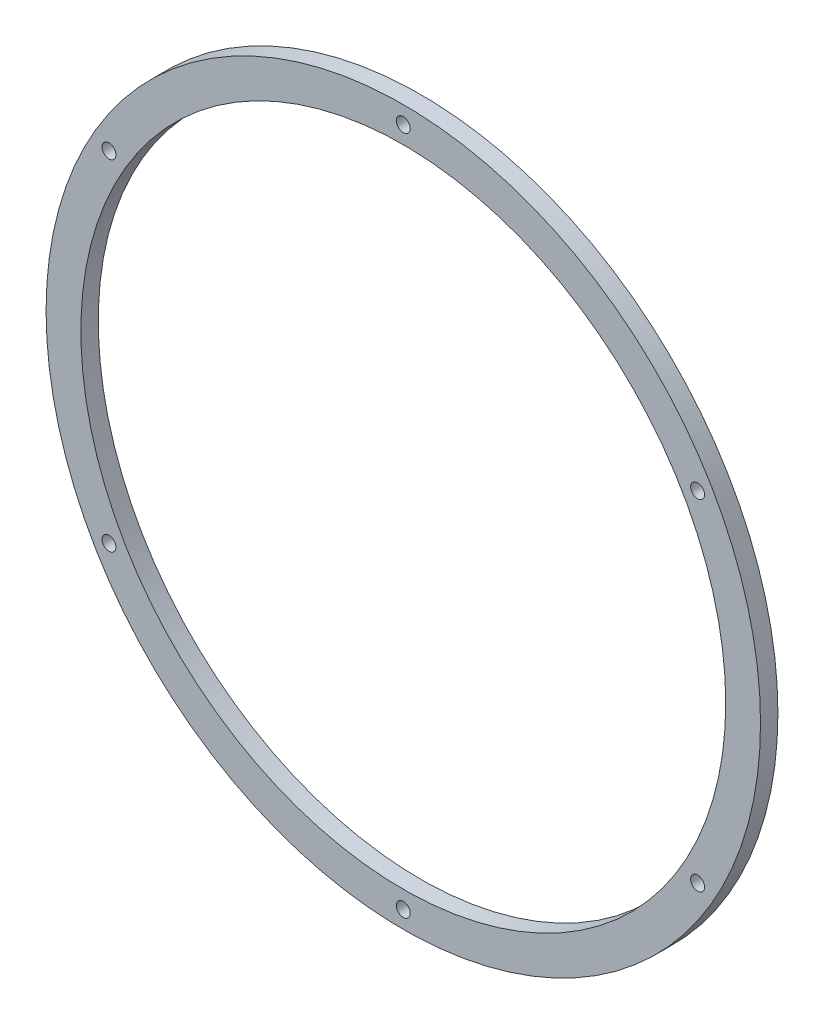
SolidWorks part; units mm, degrees
material "Brass"
ref_plane "Front Plane" through (0, 0, 0) normal (0, 0, 1) x (1, 0, 0)
ref_plane "Top Plane" through (0, 0, 0) normal (0, 1, 0) x (1, 0, 0)
ref_plane "Right Plane" through (0, 0, 0) normal (1, 0, 0) x (0, 0, -1)
sketch "Sketch1" plane through (0, 0, 0) normal (0, 0, 1) x (1, 0, 0)
  circle A0 centre (0, 0) radius 185.4
  circle A1 centre (0, 0) radius 205.4
  dimension "D1" = 370.8
  dimension "D2" = 410.8
extrude "Body" add sketch "Sketch1" along normal mid plane 10
sketch "Sketch2" plane through (0, 0, 5) normal (0, 0, 1) x (1, 0, 0)
  line L0 (0, -71.4075) -> (0, 70.4111) construction
  circle A0 centre (0, 195.4) radius 4
  circle A1 centre (0, 0) radius 195.4 construction
  dimension "D1" = 8
  dimension "D2" = 390.8
extrude "Cut-Extrude1" cut sketch "Sketch2" against normal through all
pattern_circular "Holes" count 6 over 360 about axis through (0, 0, 0) along (0, 0, 1) of "Cut-Extrude1"
